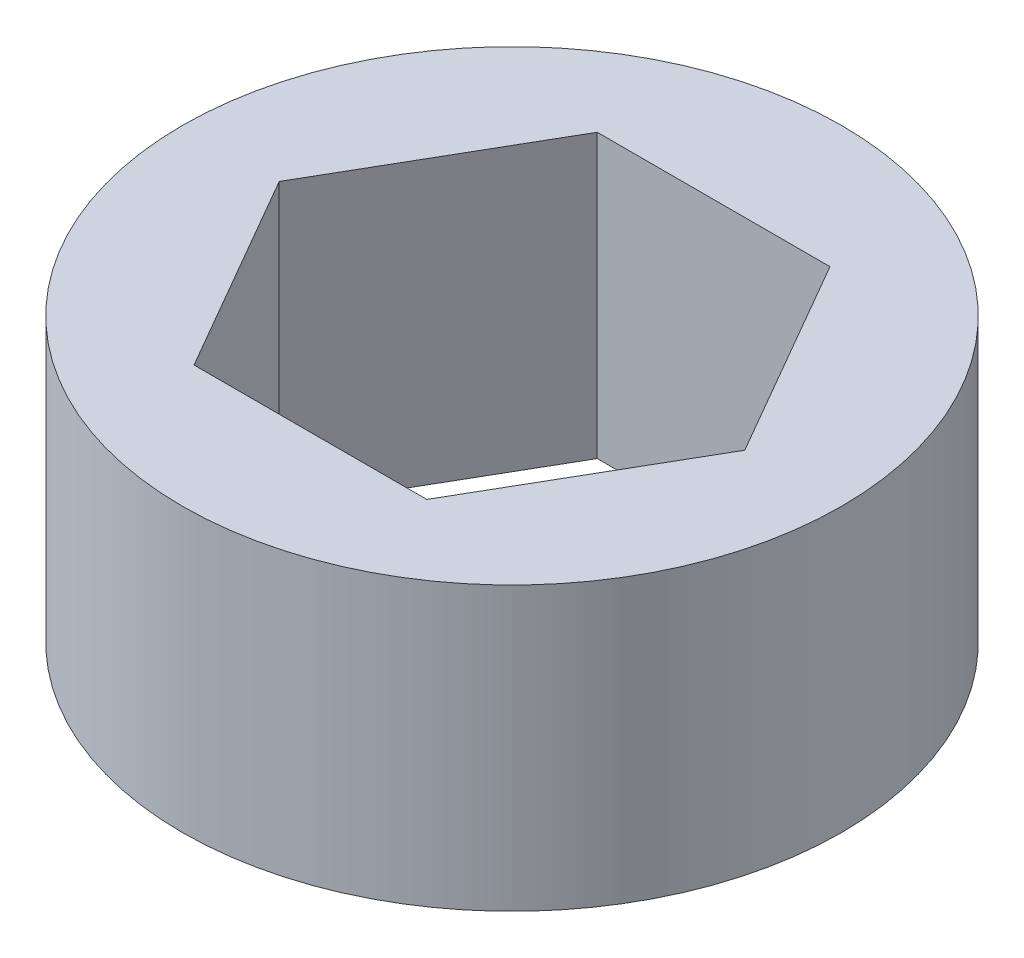
SolidWorks part; units mm, degrees
ref_plane "Front" through (0, 0, 0) normal (0, 0, 1) x (1, 0, 0)
ref_plane "Top" through (0, 0, 0) normal (0, 1, 0) x (1, 0, 0)
ref_plane "Right" through (0, 0, 0) normal (1, 0, 0) x (0, 0, -1)
sketch "Sketch1" plane through (0, 0, 0) normal (0, 1, 0) x (1, 0, 0)
  line L1 (7.8456, 0) -> (3.9228, 6.7945)
  line L2 (3.9228, 6.7945) -> (-3.9228, 6.7945)
  line L3 (-3.9228, 6.7945) -> (-7.8456, 0)
  line L4 (-7.8456, 0) -> (-3.9228, -6.7945)
  line L5 (-3.9228, -6.7945) -> (3.9228, -6.7945)
  line L6 (3.9228, -6.7945) -> (7.8456, 0)
  circle A0 centre (0, 0) radius 6.7945 construction
  circle A1 centre (0, 0) radius 11.1125
  dimension "D1" = 22.225
extrude "Boss-Extrude1" add sketch "Sketch1" along normal blind 9.525
